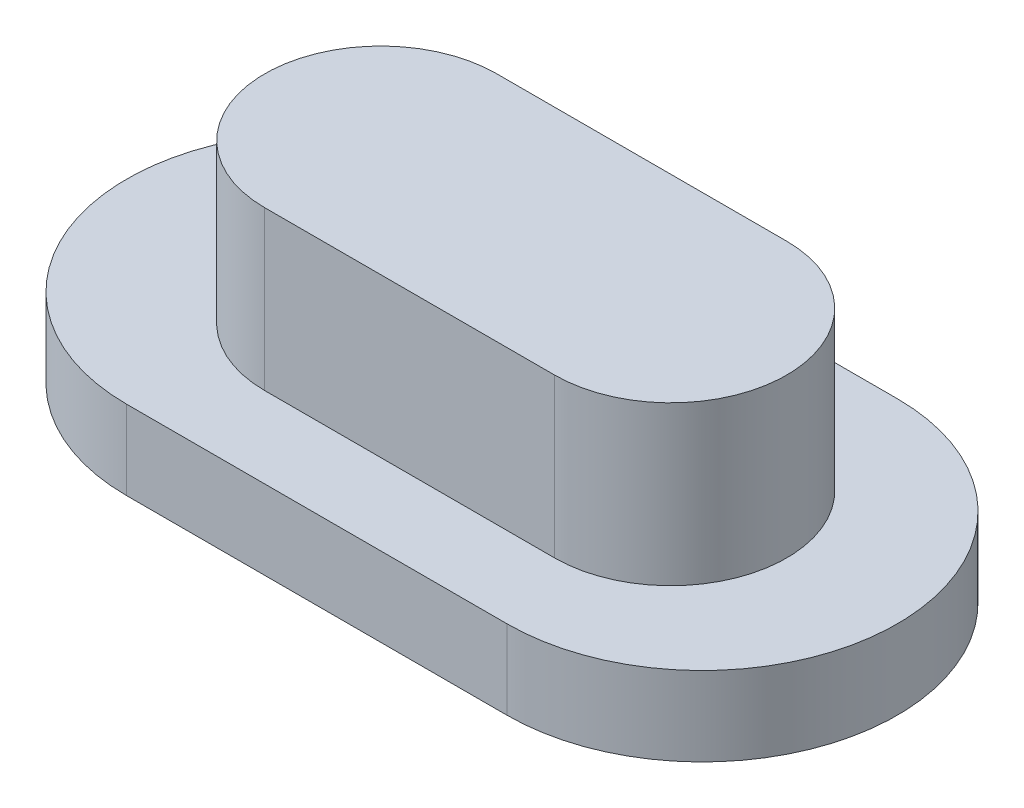
SolidWorks part; units mm, degrees
material "ABS"
ref_plane "前视基准面" through (0, 0, 0) normal (0, 0, 1) x (1, 0, 0)
ref_plane "上视基准面" through (0, 0, 0) normal (0, 1, 0) x (1, 0, 0)
ref_plane "右视基准面" through (0, 0, 0) normal (1, 0, 0) x (0, 0, -1)
other "Configuration Table"
sketch "草图1" plane through (0, 0, 0) normal (0, 1, 0) x (1, 0, 0)
  line L0 (-10.3642, -3.972) -> (-0.7574, -3.972) construction
  line L1 (-10.3642, 0.9536) -> (-0.7574, 0.9536)
  line L2 (-10.3642, -8.8976) -> (-0.7574, -8.8976)
  arc A0 (-10.3642, 0.9536) -> (-10.3642, -8.8976) centre (-10.3642, -3.972) ccw
  arc A1 (-0.7574, -8.8976) -> (-0.7574, 0.9536) centre (-0.7574, -3.972) ccw
  point P2 (-5.5608, -3.972)
  point P7 (-0.7574, -8.8976)
extrude "凸台-拉伸1" add sketch "草图1" along normal blind 2
sketch "草图2" plane through (0, 2, 0) normal (0, 1, 0) x (1, 0, 0)
  line L0 (-8.9205, -3.9274) -> (-1.5976, -3.9274) construction
  line L1 (-8.9205, -0.9982) -> (-1.5976, -0.9982)
  line L2 (-8.9205, -6.8565) -> (-1.5976, -6.8565)
  arc A0 (-8.9205, -0.9982) -> (-8.9205, -6.8565) centre (-8.9205, -3.9274) ccw
  arc A1 (-1.5976, -6.8565) -> (-1.5976, -0.9982) centre (-1.5976, -3.9274) ccw
  point P2 (-5.2591, -3.9274)
extrude "凸台-拉伸2" add sketch "草图2" along normal blind 4 contours L1 A1 L2 A0
